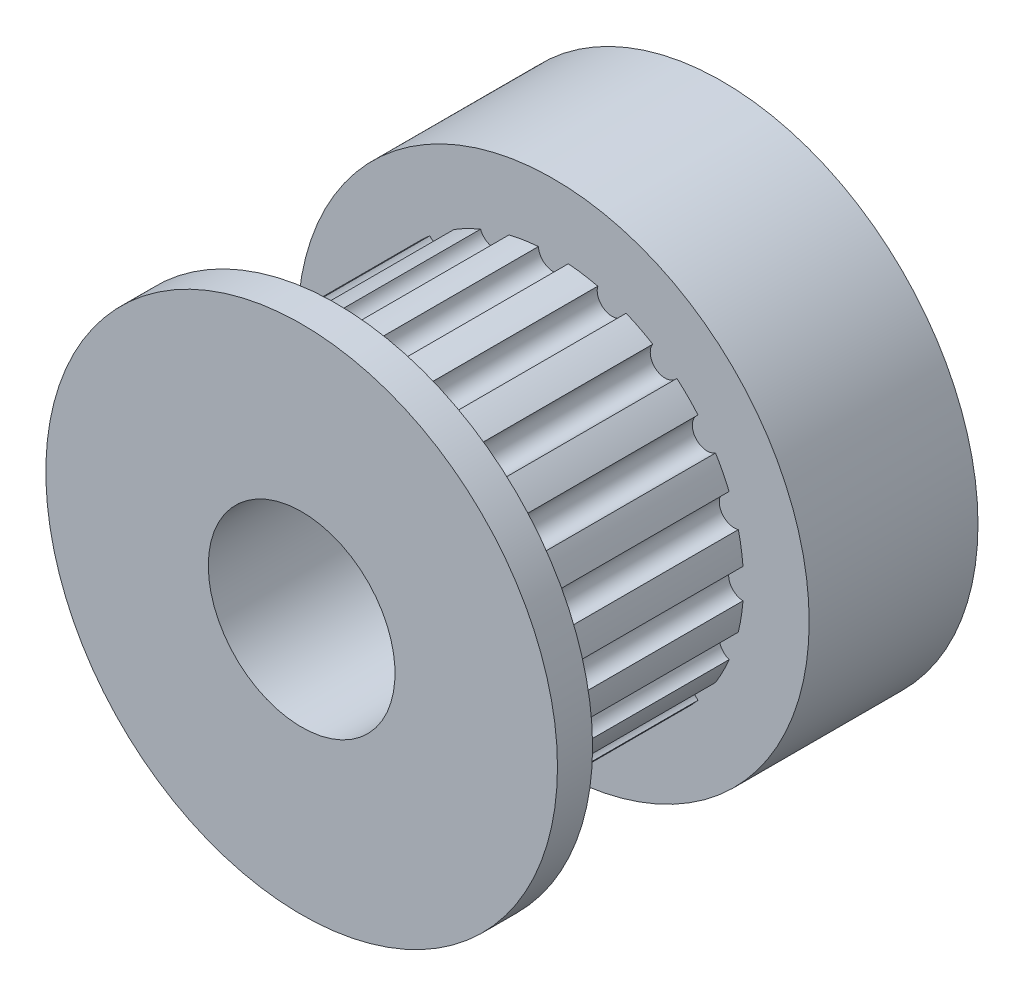
SolidWorks part; units mm, degrees
ref_plane "Plan de face" through (0, 0, 0) normal (0, 0, 1) x (1, 0, 0)
ref_plane "Plan de dessus" through (0, 0, 0) normal (0, 1, 0) x (1, 0, 0)
ref_plane "Plan de droite" through (0, 0, 0) normal (1, 0, 0) x (0, 0, -1)
sketch "Sketch1" plane through (0, 0, 0) normal (0, 0, 1) x (1, 0, 0)
  circle A0 centre (0, 0) radius 8.6995
  dimension "D1" = 17.399
extrude "Boss-Extrude1" add sketch "Sketch1" along normal blind 5.7404
sketch "Sketch2" plane through (0, 0, 5.7404) normal (0, 0, 1) x (1, 0, 0)
  circle A0 centre (0, 0) radius 6.4681
  dimension "D1" = 12.9361
extrude "Boss-Extrude2" add sketch "Sketch2" along normal blind 7.366
sketch "Sketch3" plane through (0, 0, 13.1064) normal (0, 0, 1) x (1, 0, 0)
  line L0 (0, -55) -> (0, 55) construction
  circle A0 centre (0, 6.4681) radius 0.508
  circle A1 centre (0, 0) radius 6.4681 construction
  dimension "D1" = 1.016
extrude "Cut-Extrude1" cut sketch "Sketch3" against normal up to surface (7.366 mm away) up to face at (6.4681, 0, 5.7404)
pattern_circular "CirPattern1" count 20 over 360 about axis through (0, 0, 0) along (0, 0, 1) of "Cut-Extrude1"
sketch "Sketch4" plane through (0, 0, 13.1064) normal (0, 0, 1) x (1, 0, 0)
  circle A0 centre (0, 0) radius 8.6995
  dimension "D1" = 17.399
extrude "Boss-Extrude3" add sketch "Sketch4" along normal blind 1.1938
sketch "Sketch5" plane through (0, 0, 0) normal (0, 0, -1) x (-1, 0, 0)
  circle A0 centre (0, 0) radius 3.175
  dimension "D1" = 6.35
extrude "Cut-Extrude2" cut sketch "Sketch5" against normal through all
sketch "Sketch6" plane through (0, 0, 0) normal (0, 0, -1) x (-1, 0, 0)
  circle A0 centre (0, 0) radius 8.6995
